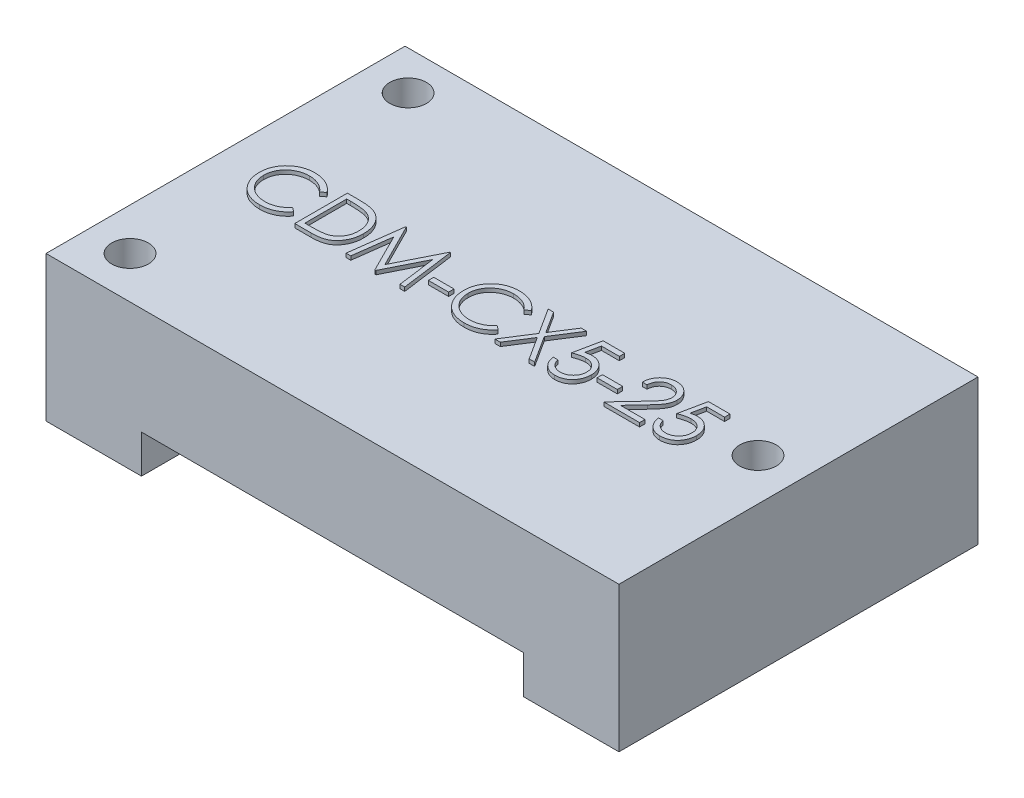
SolidWorks part; units mm, degrees
ref_plane "Front Plane" through (0, 0, 0) normal (0, 0, 1) x (1, 0, 0)
ref_plane "Top Plane" through (0, 0, 0) normal (0, 1, 0) x (1, 0, 0)
ref_plane "Right Plane" through (0, 0, 0) normal (1, 0, 0) x (0, 0, -1)
sketch "Sketch1" plane through (0, 0, 0) normal (0, 1, 0) x (1, 0, 0)
  line L1 (-19.05, 11.938) -> (19.05, 11.938)
  line L2 (-19.05, 11.938) -> (-19.05, -11.938)
  line L3 (-19.05, -11.938) -> (19.05, -11.938)
  line L4 (19.05, 11.938) -> (19.05, -11.938)
  line L5 (-19.05, 11.938) -> (19.05, -11.938) construction
  line L6 (-19.05, -11.938) -> (19.05, 11.938) construction
  circle A0 centre (-16.256, 9.3472) radius 1.2192
  circle A1 centre (-16.256, -9.144) radius 1.2192
  circle A2 centre (16.256, 0.1016) radius 1.2192
  point P0 (0, 0)
  dimension "D3" = 2.4384
  dimension "D4" = 2.4384
  dimension "D5" = 2.4384
  dimension "D1" = 38.1
  dimension "D2" = 23.876
  dimension "D6" = 18.4912
  dimension "D7" = 2.794
  dimension "D8" = 2.794
  dimension "D9" = 32.512
  dimension "D10" = 12.0396
  dimension "D11" = 2.794
extrude "Boss-Extrude1" add sketch "Sketch1" against normal blind 9.652
sketch "Sketch2" plane through (0, 0, 0) normal (0, 1, 0) x (1, 0, 0)
  text T0 "CDM-CX5-25"
extrude "Boss-Extrude2" add sketch "Sketch2" along normal blind 0.254
ref_plane "Plane1" through (0, 0, 6.35) normal (0, 0, 1) x (1, 0, 0)
sketch "Sketch4" plane through (0, 0, 0) normal (0, 0, 1) x (1, 0, 0)
  line L0 (-19.05, -9.652) -> (19.05, -9.652) construction
  line L1 (12.7, -7.112) -> (-12.7, -7.112)
  line L2 (12.7, -7.112) -> (12.7, -9.652)
  line L3 (12.7, -9.652) -> (-12.7, -9.652)
  line L4 (-12.7, -7.112) -> (-12.7, -9.652)
  line L5 (0, 0) -> (0, -7.112) construction
  dimension "D1" = 2.54
  dimension "D2" = 25.4
extrude "Cut-Extrude1" cut sketch "Sketch4" against normal through all both and the other way through all
sketch "Sketch5" plane through (0, 0, 6.35) normal (0, 0, 1) x (1, 0, 0)
  line L1 (17.4752, 0) -> (15.0368, 0) construction
  line L2 (17.4752, 0) -> (15.0368, 0) construction
  line L3 (16.256, 0) -> (16.256, -9.652) construction
  line L4 (15.0368, -9.652) -> (17.4752, -9.652) construction
  line L5 (11.938, -3.048) -> (16.256, -3.048) construction
  point P0 (11.938, -3.048)
  dimension "D1" = 4.318
  dimension "D2" = 6.604
